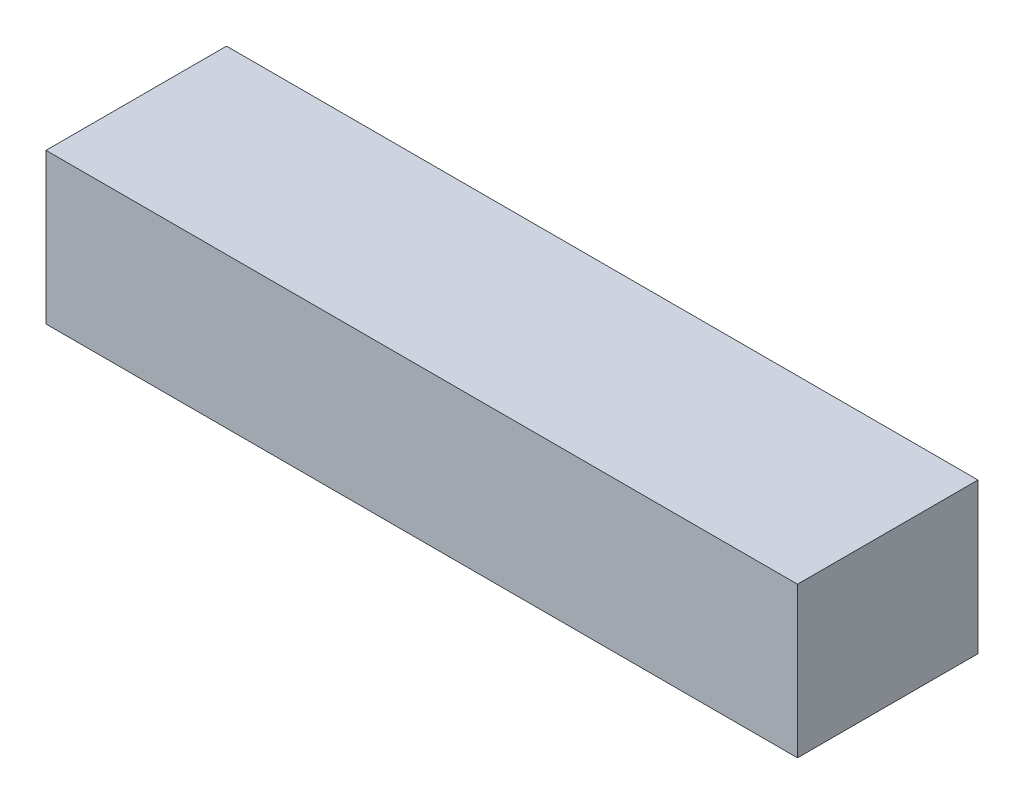
SolidWorks part; units mm, degrees
ref_plane "Plan de face" through (0, 0, 0) normal (0, 0, 1) x (1, 0, 0)
ref_plane "Plan de dessus" through (0, 0, 0) normal (0, 1, 0) x (1, 0, 0)
ref_plane "Plan de droite" through (0, 0, 0) normal (1, 0, 0) x (0, 0, -1)
sketch "Esquisse1" plane through (0, 0, 0) normal (0, 0, 1) x (1, 0, 0)
  line L1 (-11.1757, 1.405) -> (13.8043, 1.405)
  line L2 (-11.1757, 1.405) -> (-11.1757, -3.595)
  line L3 (-11.1757, -3.595) -> (13.8043, -3.595)
  line L4 (13.8043, 1.405) -> (13.8043, -3.595)
  dimension "D1" = 5
  dimension "D2" = 24.98
extrude "Boss.-Extru.1" add sketch "Esquisse1" along normal blind 6
